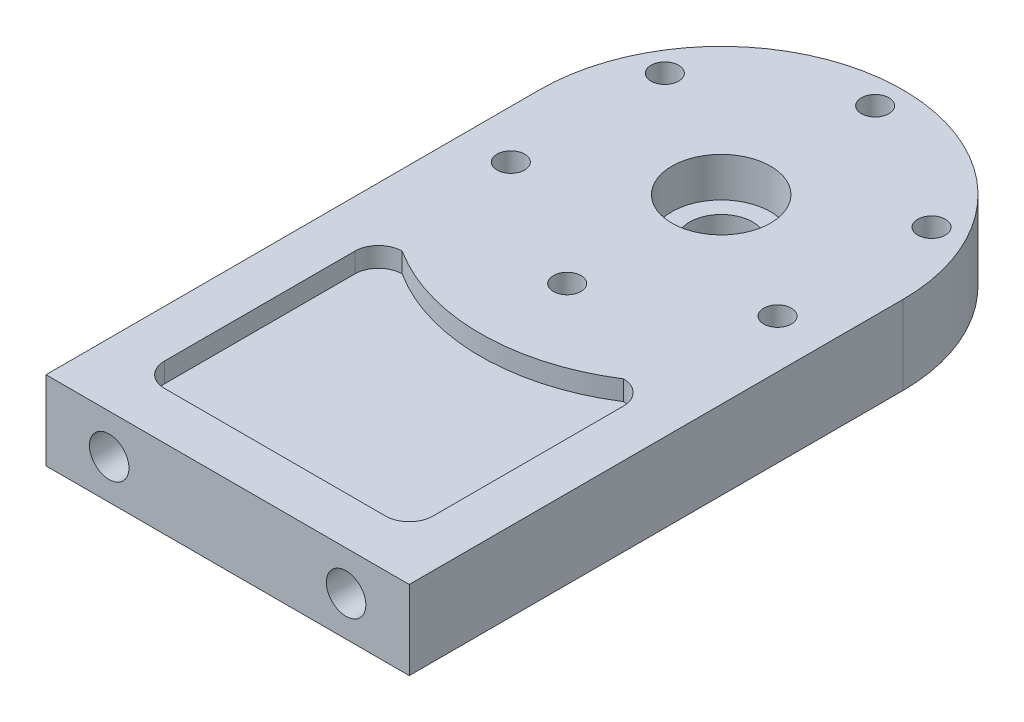
SolidWorks part; units mm, degrees
ref_plane "Front Plane" through (0, 0, 0) normal (0, 0, 1) x (1, 0, 0)
ref_plane "Top Plane" through (0, 0, 0) normal (0, 1, 0) x (1, 0, 0)
ref_plane "Right Plane" through (0, 0, 0) normal (1, 0, 0) x (0, 0, -1)
sketch "Sketch3" plane through (0, 0, 0) normal (0, 1, 0) x (1, 0, 0)
  line L1 (0, 0) -> (184, 0)
  line L2 (0, 0) -> (0, 250)
  line L3 (0, 250) -> (184, 250) construction
  line L4 (184, 0) -> (184, 250)
  arc A0 (184, 250) -> (0, 250) centre (92, 250) ccw
  circle A1 centre (92, 250) radius 78 construction
  dimension "D3" = 156
  dimension "D1" = 250
  dimension "D2" = 184
extrude "Boss-Extrude1" add sketch "Sketch3" along normal blind 40
sketch "Sketch5" plane through (0, 40, 0) normal (0, 1, 0) x (1, 0, 0)
  circle A0 centre (92, 250) radius 25
  dimension "D1" = 50
extrude "Cut-Extrude1" cut sketch "Sketch5" against normal blind 20
sketch "Sketch6" plane through (0, 0, 0) normal (0, -1, 0) x (1, 0, 0)
  circle A0 centre (92, -250) radius 16
  dimension "D1" = 32
extrude "Cut-Extrude2" cut sketch "Sketch6" against normal blind 20
sketch "Sketch7" plane through (0, 40, 0) normal (0, 1, 0) x (1, 0, 0)
  circle A0 centre (92, 250) radius 78 construction
  circle A1 centre (92, 328) radius 7
  dimension "D1" = 156
  dimension "D2" = 14
extrude "Cut-Extrude3" cut sketch "Sketch7" against normal blind 25
pattern_circular "CirPattern1" count 6 over 360 about axis through (92, 0, -250) along (0, 1, 0) of "Cut-Extrude3"
sketch "Sketch8" plane through (0, 0, 0) normal (0, -1, 0) x (1, 0, 0)
  circle A0 centre (92, -250) radius 78 construction
  circle A1 centre (92, -328) radius 12
  dimension "D1" = 156
  dimension "D2" = 24
extrude "Cut-Extrude4" cut sketch "Sketch8" against normal blind 15
pattern_circular "CirPattern2" count 6 over 360 about axis through (92, 0, -250) along (0, 1, 0) of "Cut-Extrude4"
sketch "Sketch9" plane through (0, 40, 0) normal (0, 1, 0) x (1, 0, 0)
  line L0 (0, 250) -> (0, 0) construction
  line L1 (36, 24) -> (148, 24)
  line L2 (24, 36) -> (24, 132.4208)
  line L3 (36, 144.4208) -> (148, 144.4208) construction
  line L4 (160, 36) -> (160, 132.4208)
  line L5 (184, 0) -> (184, 250) construction
  line L6 (0, 0) -> (184, 0) construction
  arc A0 (24, 36) -> (36, 24) centre (36, 36) ccw
  arc A1 (148, 24) -> (160, 36) centre (148, 36) ccw
  arc A2 (160, 132.4208) -> (148, 144.4208) centre (148, 132.4208) ccw
  arc A3 (24, 132.4208) -> (36, 144.4208) centre (36, 132.4208) cw
  arc A4 (148, 144.4208) -> (36, 144.4208) centre (92, 232.0564) cw
  dimension "D5" = 12
  dimension "D6" = 104
  dimension "D1" = 24
  dimension "D2" = 24
  dimension "D3" = 24
  dimension "D4" = 144.4208
extrude "Cut-Extrude5" cut sketch "Sketch9" against normal blind 10
ref_plane "Plane1" through (0, 20, 0) normal (0, 1, 0) x (1, 0, 0)
mirror "Mirror1" about plane through (0, 20, 0) normal (0, 1, 0) of "Cut-Extrude5"
ref_plane "Plane2" through (92, 0, 0) normal (1, 0, 0) x (0, 0, -1)
sketch "Sketch13" plane through (0, 0, 0) normal (0, 0, 1) x (1, 0, 0)
  line L0 (92, 0) -> (92, 40) construction
  line L1 (0, 0) -> (184, 0) construction
  line L2 (0, 40) -> (184, 40) construction
  circle A0 centre (32, 20) radius 10
  circle A1 centre (152, 20) radius 10
  dimension "D1" = 20
  dimension "D2" = 60
  dimension "D3" = 20
extrude "Cut-Extrude10" cut sketch "Sketch13" against normal blind 20
